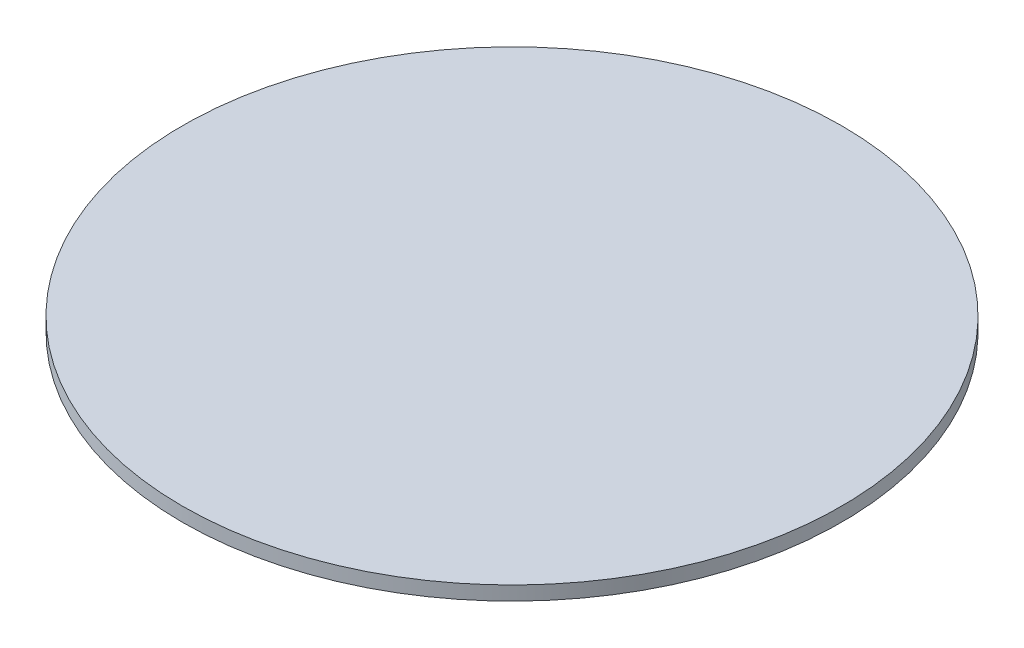
SolidWorks part; units mm, degrees
ref_plane "Front Plane" through (0, 0, 0) normal (0, 0, 1) x (1, 0, 0)
ref_plane "Top Plane" through (0, 0, 0) normal (0, 1, 0) x (1, 0, 0)
ref_plane "Right Plane" through (0, 0, 0) normal (1, 0, 0) x (0, 0, -1)
sketch "Sketch1" plane through (0, 0, 0) normal (0, 1, 0) x (1, 0, 0)
  circle A0 centre (0, 0) radius 40
extrude "Boss-Extrude1" add sketch "Sketch1" along normal blind 1.7
scale "Scale2" scale about centroid uniform scaling yes scale factor 0.5
